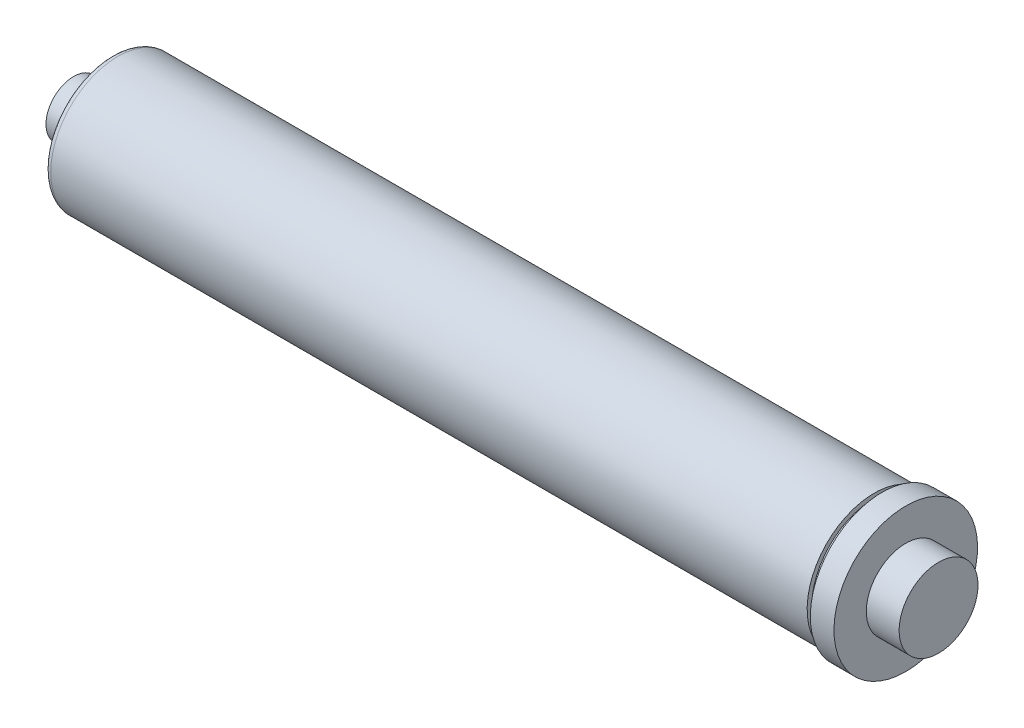
SolidWorks part; units mm, degrees
material "6061-T6 (SS)"
ref_plane "Front Plane" through (0, 0, 0) normal (0, 0, 1) x (1, 0, 0)
ref_plane "Top Plane" through (0, 0, 0) normal (0, 1, 0) x (1, 0, 0)
ref_plane "Right Plane" through (0, 0, 0) normal (1, 0, 0) x (0, 0, -1)
sketch "Sketch1" plane through (0, 0, 0) normal (0, 0, 1) x (1, 0, 0)
  line L0 (0, 0) -> (0, 11.1125)
  line L1 (0, 11.1125) -> (15.24, 11.1125)
  line L2 (15.24, 11.1125) -> (15.24, 26.9875)
  line L3 (15.24, 26.9875) -> (322.199, 26.9875)
  line L4 (322.199, 26.9875) -> (322.199, 25.1714)
  line L5 (322.199, 25.1714) -> (325.374, 25.1714)
  line L6 (325.374, 25.1714) -> (325.374, 28.8925)
  line L7 (325.374, 28.8925) -> (334.899, 28.8925)
  line L8 (334.899, 28.8925) -> (334.899, 15.875)
  line L9 (334.899, 15.875) -> (348.107, 15.875)
  line L10 (348.107, 15.875) -> (348.107, 0)
  line L11 (348.107, 0) -> (0, 0)
  line L12 (0, 0) -> (452.3115, 0) construction
  dimension "D1" = 310.134
  dimension "D2" = 15.24
  dimension "D3" = 3.175
  dimension "D4" = 9.525
  dimension "D5" = 13.208
  dimension "D6" = 15.875
  dimension "D7" = 28.8925
  dimension "D8" = 26.9875
  dimension "D9" = 11.1125
  dimension "D10" = 25.1714
revolve "Revolve1" add sketch "Sketch1" angle 360 about L12
fillet "Fillet1" radius 2.54 1 edges at (15.24, -26.9875, 0)
sketch "Sketch2" plane through (0, 0, 0) normal (-1, 0, 0) x (0, 0, 1)
  circle A1 centre (0, 0) radius 7.62
  dimension "D1" = 15.24
extrude "Cut-Extrude1" cut sketch "Sketch2" against normal blind 6.35
sketch "Sketch3" plane through (6.35, 0, 0) normal (-1, 0, 0) x (0, 0, 1)
  circle A0 centre (0, 0) radius 1.5875
  dimension "D1" = 3.175
extrude "Cut-Extrude2" cut sketch "Sketch3" against normal blind 6.35
